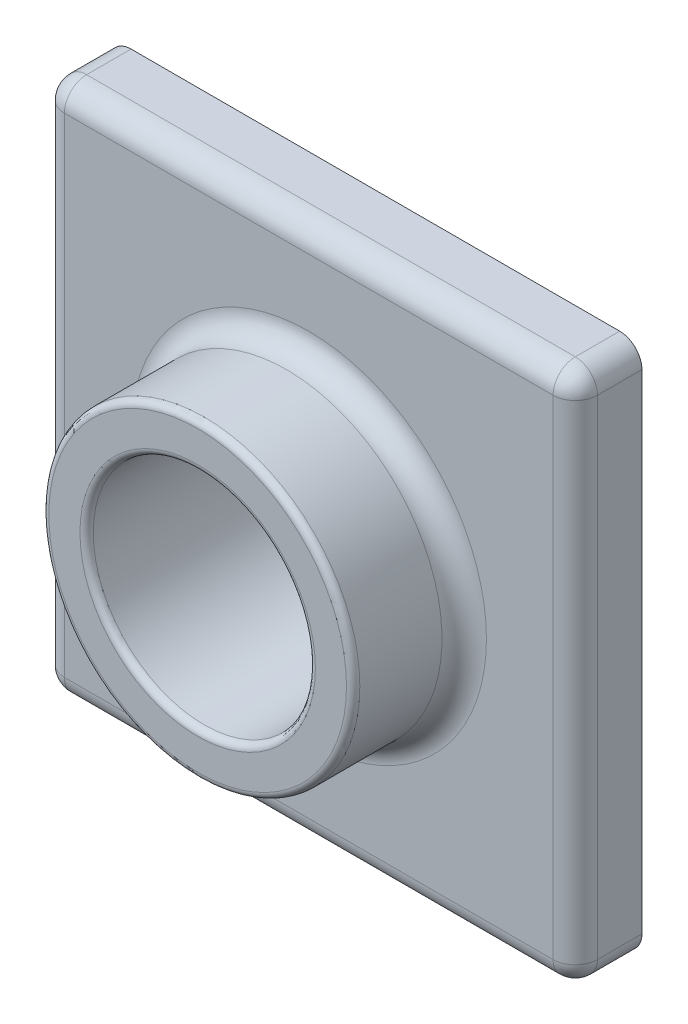
SolidWorks part; units mm, degrees
ref_plane "Front Plane" through (0, 0, 0) normal (0, 0, 1) x (1, 0, 0)
ref_plane "Top Plane" through (0, 0, 0) normal (0, 1, 0) x (1, 0, 0)
ref_plane "Right Plane" through (0, 0, 0) normal (1, 0, 0) x (0, 0, -1)
sketch "Sketch2" plane through (0, 0, 0) normal (0, 0, 1) x (1, 0, 0)
  line L1 (0, 0) -> (120, 0)
  line L2 (0, 0) -> (0, 120)
  line L3 (0, 120) -> (120, 120)
  line L4 (120, 0) -> (120, 120)
  dimension "D1" = 120
  dimension "D2" = 120
extrude "Boss-Extrude1" add sketch "Sketch2" along normal blind 15
sketch "Sketch3" plane through (0, 0, 15) normal (0, 0, 1) x (1, 0, 0)
  line L0 (120, 120) -> (0, 120) construction
  line L1 (120, 0) -> (120, 120) construction
  circle A0 centre (60, 60) radius 35
  dimension "D1" = 70
  dimension "D2" = 60
  dimension "D3" = 60
extrude "Boss-Extrude2" add sketch "Sketch3" along normal blind 25
sketch "Sketch4" plane through (0, 0, 40) normal (0, 0, 1) x (1, 0, 0)
  line L0 (0, 120) -> (0, 0) construction
  line L1 (120, 120) -> (0, 120) construction
  circle A0 centre (60, 60) radius 25
  dimension "D1" = 50
  dimension "D2" = 60
  dimension "D3" = 60
extrude "Cut-Extrude1" cut sketch "Sketch4" against normal through all
fillet "Fillet1" radius 5 9 edges at (25, 60, 15) (60, 120, 15) (120, 60, 15) (60, 0, 15) (0, 60, 15) (0, 0, 7.5) (120, 0, 7.5) (120, 120, 7.5) (0, 120, 7.5)
fillet "Fillet2" radius 1.5 2 edges at (95, 60, 40) (85, 60, 40)
shell "Shell1" thickness 2
ref_plane "Plane1" through (115, 5, 15) normal (0, 1, 0) x (1, 0, 0)
